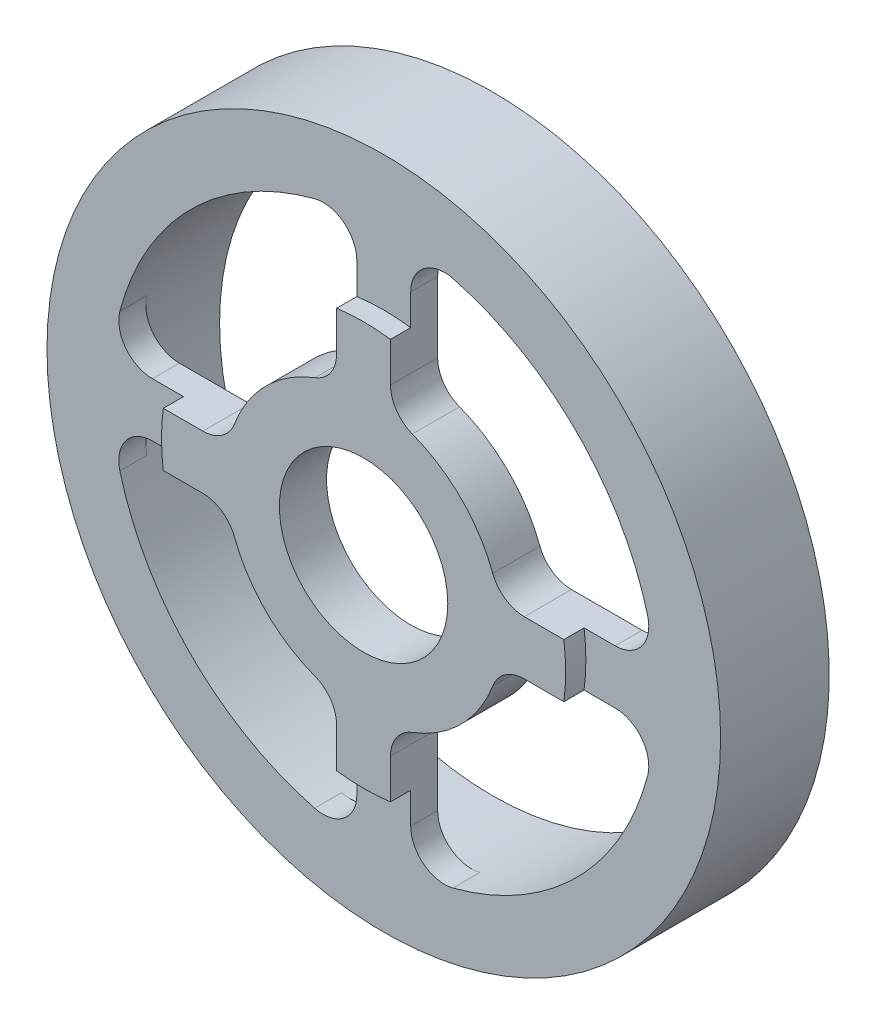
SolidWorks part; units mm, degrees
material "7075-T6 (SN)"
ref_plane "Front" through (0, 0, 0) normal (0, 0, 1) x (1, 0, 0)
ref_plane "Top" through (0, 0, 0) normal (0, 1, 0) x (1, 0, 0)
ref_plane "Right" through (0, 0, 0) normal (1, 0, 0) x (0, 0, -1)
sketch "Esquisse1" plane through (0, 0, 0) normal (0, 0, 1) x (1, 0, 0)
  circle A0 centre (0, 0) radius 50
  circle A1 centre (0, 0) radius 12.5
  dimension "D1" = 100
  dimension "D2" = 25
extrude "Boss.-Extru.1" add sketch "Esquisse1" along normal blind 4
sketch "Esquisse2" plane through (0, 0, 4) normal (0, 0, 1) x (1, 0, 0)
  circle A0 centre (0, 0) radius 12.5
  circle A1 centre (0, 0) radius 30
  dimension "D1" = 60
extrude "Boss.-Extru.2" add sketch "Esquisse2" along normal blind 3
sketch "Esquisse4" plane through (0, 0, 0) normal (0, 0, -1) x (-1, 0, 0)
  line L0 (0, 50) -> (0, -56.9306) construction
  line L1 (-50, 0) -> (69.0887, 0) construction
  line L2 (0, 0) -> (-67.6766, 67.6766) construction
  line L3 (-4, 23.859) -> (-4, 34.3402)
  line L4 (4, 23.859) -> (4, 34.3402)
  line L5 (-23.859, -4) -> (-34.3402, -4)
  line L6 (-23.859, 4) -> (-34.3402, 4)
  line L7 (23.859, -4) -> (34.3402, -4)
  line L8 (23.859, 4) -> (34.3402, 4)
  line L9 (-4, -23.859) -> (-4, -34.3402)
  line L10 (4, -23.859) -> (4, -34.3402)
  arc A0 (-39.1769, -10.2676) -> (-10.2676, -39.1769) centre (0, 0) ccw
  circle A1 centre (0, 0) radius 50 construction
  arc A2 (-19.1807, -7.2353) -> (-7.2353, -19.1807) centre (0, 0) ccw
  circle A3 centre (0, 0) radius 12.5 construction
  arc A4 (-10.2676, 39.1769) -> (-39.1769, 10.2676) centre (0, 0) ccw
  arc A5 (39.1769, 10.2676) -> (10.2676, 39.1769) centre (0, 0) ccw
  arc A6 (19.1807, 7.2353) -> (7.2353, 19.1807) centre (0, 0) ccw
  arc A7 (10.2676, -39.1769) -> (39.1769, -10.2676) centre (0, 0) ccw
  arc A8 (7.2353, -19.1807) -> (19.1807, -7.2353) centre (0, 0) ccw
  arc A9 (-23.859, 4) -> (-19.1807, 7.2353) centre (-23.859, 9) ccw
  arc A10 (-34.3402, 4) -> (-39.1769, 10.2676) centre (-34.3402, 9) cw
  arc A11 (-4, 34.3402) -> (-10.2676, 39.1769) centre (-9, 34.3402) ccw
  arc A12 (4, 34.3402) -> (10.2676, 39.1769) centre (9, 34.3402) cw
  arc A13 (34.3402, 4) -> (39.1769, 10.2676) centre (34.3402, 9) ccw
  arc A14 (23.859, 4) -> (19.1807, 7.2353) centre (23.859, 9) cw
  arc A15 (23.859, -4) -> (19.1807, -7.2353) centre (23.859, -9) ccw
  arc A16 (34.3402, -4) -> (39.1769, -10.2676) centre (34.3402, -9) cw
  arc A17 (4, -34.3402) -> (10.2676, -39.1769) centre (9, -34.3402) ccw
  arc A18 (4, -23.859) -> (7.2353, -19.1807) centre (9, -23.859) cw
  arc A19 (-4, -23.859) -> (-7.2353, -19.1807) centre (-9, -23.859) ccw
  arc A20 (-4, -34.3402) -> (-10.2676, -39.1769) centre (-9, -34.3402) cw
  arc A21 (-34.3402, -4) -> (-39.1769, -10.2676) centre (-34.3402, -9) ccw
  arc A22 (-23.859, -4) -> (-19.1807, -7.2353) centre (-23.859, -9) cw
  arc A23 (-7.2353, 19.1807) -> (-19.1807, 7.2353) centre (0, 0) ccw
  arc A24 (4, 23.859) -> (7.2353, 19.1807) centre (9, 23.859) ccw
  arc A25 (-4, 23.859) -> (-7.2353, 19.1807) centre (-9, 23.859) cw
  point P31 (-20.106, 4)
  point P34 (-40.302, 4)
  point P37 (-4, 40.302)
  point P40 (4, 40.302)
  point P43 (40.302, 4)
  point P46 (20.106, 4)
  point P49 (20.106, -4)
  point P52 (40.302, -4)
  point P55 (4, -40.302)
  point P58 (4, -20.106)
  point P61 (-4, -20.106)
  point P64 (-4, -40.302)
  point P67 (-40.302, -4)
  point P70 (-20.106, -4)
  point P73 (4, 20.106)
  point P76 (-4, 20.106)
  dimension "D1" = 8
  dimension "D3" = 45
  dimension "D2" = 20
  dimension "D4" = 4
  dimension "D5" = 5
  dimension "D6" = 5
extrude "Enlèv. mat.-Extru.1" cut sketch "Esquisse4" against normal blind 23
sketch "Esquisse5" plane through (0, 0, 0) normal (0, 0, -1) x (-1, 0, 0)
  circle A0 centre (0, 0) radius 50
  circle A1 centre (0, 0) radius 40.5
extrude "Boss.-Extru.3" add sketch "Esquisse5" along normal blind 12.125
